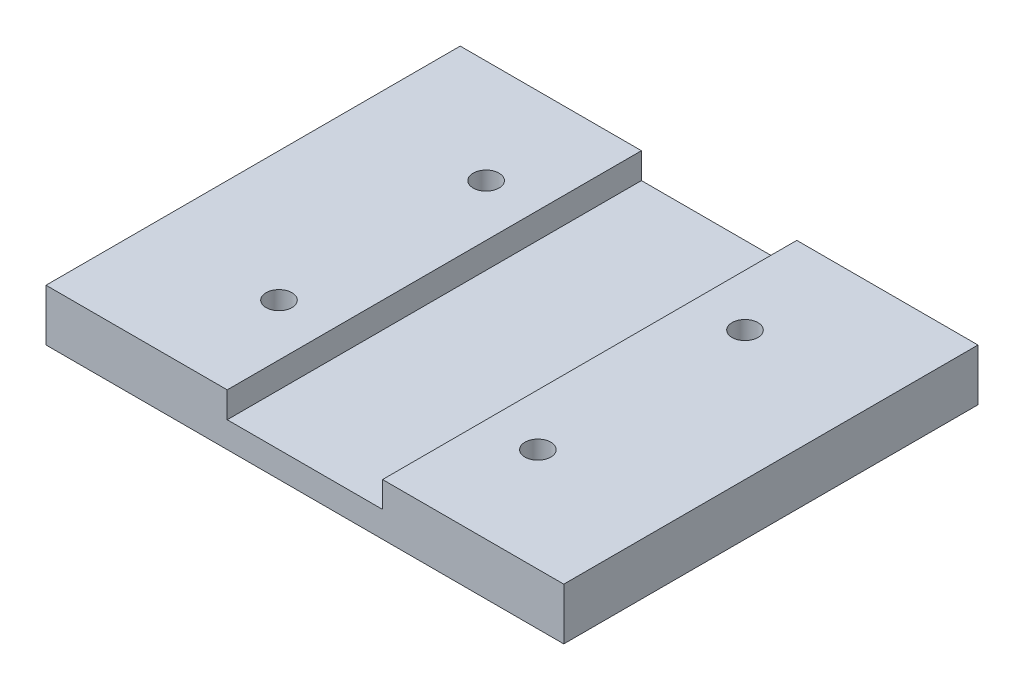
SolidWorks part; units mm, degrees
ref_plane "Front Plane" through (0, 0, 0) normal (0, 0, 1) x (1, 0, 0)
ref_plane "Top Plane" through (0, 0, 0) normal (0, 1, 0) x (1, 0, 0)
ref_plane "Right Plane" through (0, 0, 0) normal (1, 0, 0) x (0, 0, -1)
sketch "Sketch1" plane through (0, 0, 0) normal (0, 1, 0) x (1, 0, 0)
  line L1 (-1270, -1016) -> (1270, -1016)
  line L2 (-1270, -1016) -> (-1270, 1016)
  line L3 (-1270, 1016) -> (1270, 1016)
  line L4 (1270, -1016) -> (1270, 1016)
  line L5 (-1270, -1016) -> (1270, 1016) construction
  line L6 (-1270, 1016) -> (1270, -1016) construction
  point P0 (0, 0)
  dimension "D1" = 2540
  dimension "D2" = 2032
extrude "Boss-Extrude1" add sketch "Sketch1" along normal blind 254
sketch "Sketch2" plane through (0, 0, 0) normal (0, 0, 1) x (1, 0, 0)
  line L0 (-381, 254) -> (-381, 127)
  line L1 (-1270, 254) -> (1270, 254) construction
  line L2 (-381, 127) -> (381, 127)
  line L3 (381, 127) -> (381, 254)
  line L4 (0, -139.7) -> (0, 139.7) construction
  line L5 (-381, 254) -> (381, 254)
  dimension "D1" = 127
  dimension "D2" = 381
  dimension "D3" = 381
extrude "Cut-Extrude1" cut sketch "Sketch2" against normal through all both and the other way through all contours L2 L3 L5 L0
hole_wizard "5\" Diameter Hole1" positions "Sketch3" profile "Sketch4" hole size "#97" standard "ANSI Inch" end condition through all
sketch "Sketch3" plane through (0, 254, 0) normal (0, 1, 0) x (1, 0, 0)
  line L0 (-381, 1016) -> (-381, -1016) construction
  line L1 (-139.7, 0) -> (139.7, 0) construction
  point P0 (-635, 508)
  point P2 (-635, -508)
  dimension "D1" = 254
  dimension "D2" = 508
  dimension "D3" = 254
  dimension "D4" = 508
sketch "Sketch4" plane through (-635, 254, -508) normal (1, 0, 0) x (0, 0, 1)
  line L0 (0, 0) -> (0, 254)
  line L1 (0, 254) -> (63.5, 254)
  line L2 (63.5, 254) -> (63.5, 0)
  line L5 (63.5, 0) -> (0, 0)
  line L11 (0, -6.35) -> (0, 107.95) construction
  dimension "Thru Hole Dia." = 127
  dimension "Thru Hole Depth" = 254
mirror "Mirror1" about plane through (0, 0, 0) normal (1, 0, 0) of "5\" Diameter Hole1"
